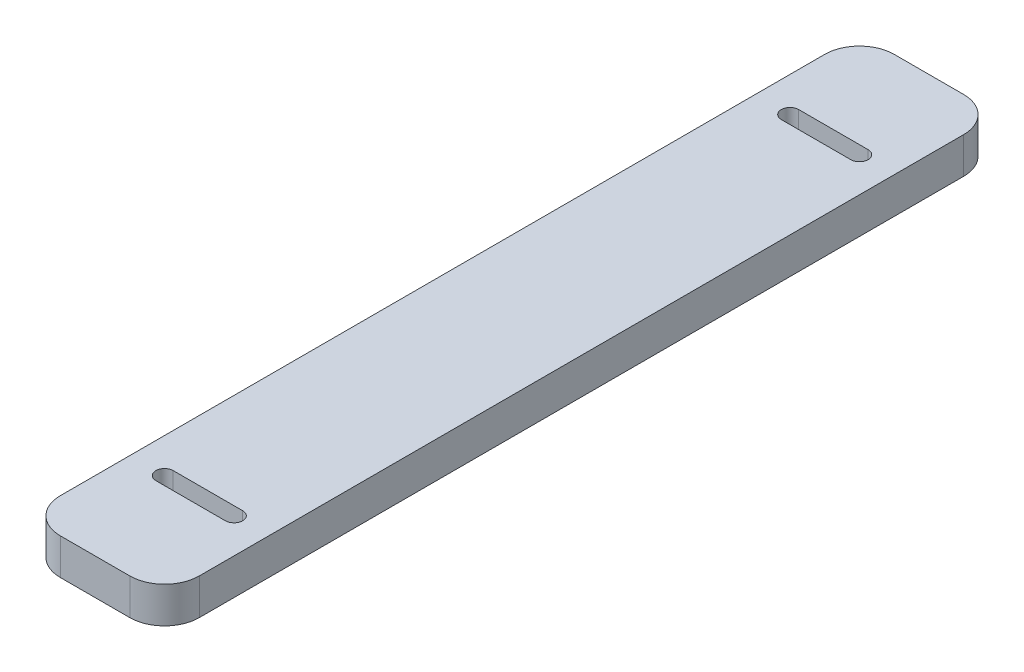
SolidWorks part; units mm, degrees
material "Acrylic (BLUE)"
ref_plane "Front Plane" through (0, 0, 0) normal (0, 0, 1) x (1, 0, 0)
ref_plane "Top Plane" through (0, 0, 0) normal (0, 1, 0) x (1, 0, 0)
ref_plane "Right Plane" through (0, 0, 0) normal (1, 0, 0) x (0, 0, -1)
sketch "Sketch1" plane through (0, 0, 0) normal (0, 1, 0) x (1, 0, 0)
  line L0 (-12.7, 76.2) -> (12.7, -76.2) construction
  line L1 (-12.7, 76.2) -> (12.7, 76.2)
  line L2 (-12.7, 76.2) -> (-12.7, -76.2)
  line L3 (-12.7, -76.2) -> (12.7, -76.2)
  line L4 (12.7, 76.2) -> (12.7, -76.2)
  dimension "D1" = 25.4
  dimension "D2" = 152.4
extrude "Boss-Extrude1" add sketch "Sketch1" along normal blind 6.604
sketch "Sketch2" plane through (0, 6.604, 0) normal (0, 1, 0) x (1, 0, 0)
  line L0 (0, 0) -> (0, 57.15) construction
  line L1 (-6.35, 57.15) -> (6.35, 57.15) construction
  line L2 (-6.35, 58.7375) -> (6.35, 58.7375)
  line L3 (-6.35, 55.5625) -> (6.35, 55.5625)
  line L4 (0, 0) -> (0, -57.15) construction
  line L5 (-6.35, -57.15) -> (6.35, -57.15) construction
  line L6 (-6.35, -55.5625) -> (6.35, -55.5625)
  line L7 (-6.35, -58.7375) -> (6.35, -58.7375)
  arc A0 (-6.35, 58.7375) -> (-6.35, 55.5625) centre (-6.35, 57.15) ccw
  arc A1 (6.35, 55.5625) -> (6.35, 58.7375) centre (6.35, 57.15) ccw
  arc A2 (-6.35, -55.5625) -> (-6.35, -58.7375) centre (-6.35, -57.15) ccw
  arc A3 (6.35, -58.7375) -> (6.35, -55.5625) centre (6.35, -57.15) ccw
  point P4 (0, 57.15)
  point P14 (0, -57.15)
  dimension "D1" = 57.15
  dimension "D2" = 3.175
  dimension "D3" = 12.7
extrude "Cut-Extrude1" cut sketch "Sketch2" against normal through all
fillet "Fillet1" radius 6.35 4 edges at (-12.7, 3.302, 76.2) (12.7, 3.302, 76.2) (-12.7, 3.302, -76.2) (12.7, 3.302, -76.2)
other "Move Face1" [suppressed] parameters "D1"=0.0508
